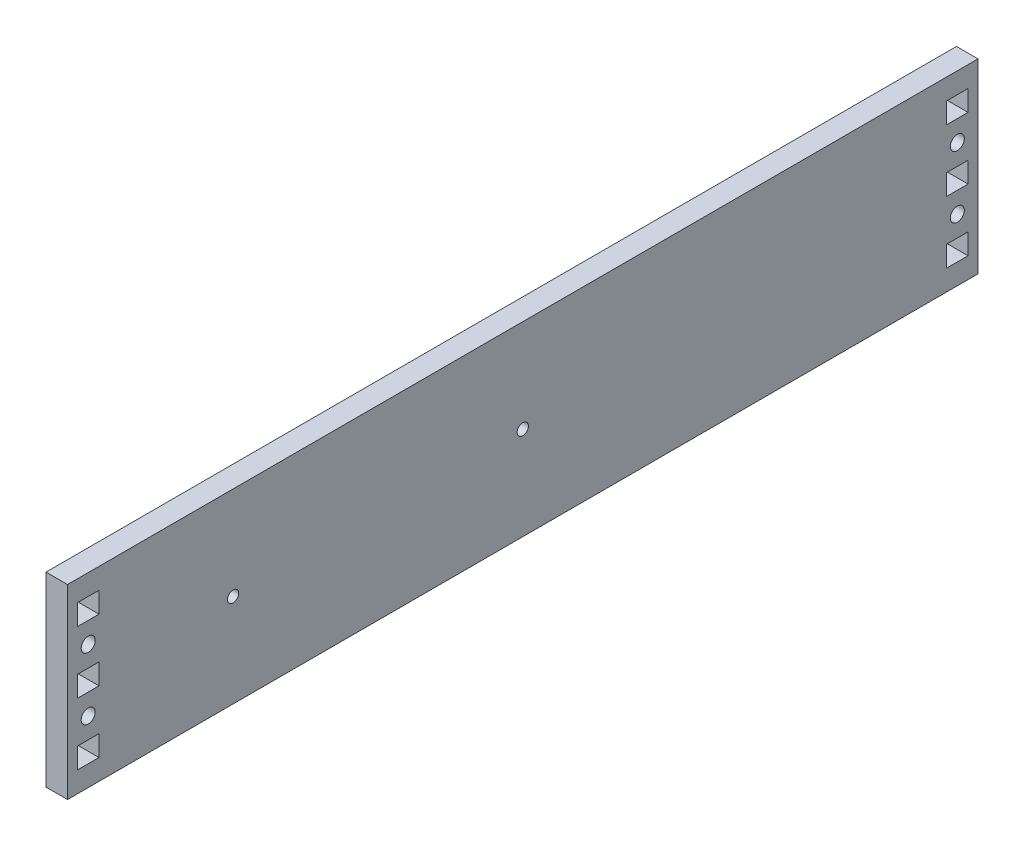
SolidWorks part; units mm, degrees
material "Acrylic (BLUE)"
ref_plane "Front Plane" through (0, 0, 0) normal (0, 0, 1) x (1, 0, 0)
ref_plane "Top Plane" through (0, 0, 0) normal (0, 1, 0) x (1, 0, 0)
ref_plane "Right Plane" through (0, 0, 0) normal (1, 0, 0) x (0, 0, -1)
sketch "Sketch1" plane through (0, 0, 0) normal (1, 0, 0) x (0, 0, -1)
  line L0 (0, 0) -> (0, 28.575) construction
  line L1 (-139.7, 28.575) -> (139.7, 28.575)
  line L2 (-139.7, 28.575) -> (-139.7, -28.575)
  line L3 (-139.7, -28.575) -> (139.7, -28.575)
  line L4 (139.7, 28.575) -> (139.7, -28.575)
  line L5 (-130.048, 0) -> (0, 0) construction
  line L6 (0, 0) -> (130.048, 0) construction
  line L7 (0, 0) -> (0, -28.575) construction
  line B0 (-130.048, 3.175) -> (-130.048, -3.175)
  line B1 (-130.048, -3.175) -> (-136.652, -3.175)
  line B2 (-136.652, -3.175) -> (-136.652, 3.175)
  line B3 (-136.652, 3.175) -> (-130.048, 3.175)
  line B4 (-130.048, 22.225) -> (-130.048, 15.875)
  line B5 (-130.048, 15.875) -> (-136.652, 15.875)
  line B6 (-136.652, 15.875) -> (-136.652, 22.225)
  line B7 (-136.652, 22.225) -> (-130.048, 22.225)
  circle B8 centre (-133.35, 9.525) radius 2.1526
  line B9 (-130.048, -15.875) -> (-130.048, -22.225)
  line B10 (-130.048, -22.225) -> (-136.652, -22.225)
  line B11 (-136.652, -15.875) -> (-136.652, -22.225)
  line B12 (-130.048, -15.875) -> (-136.652, -15.875)
  circle B13 centre (-133.35, -9.525) radius 2.1527
  line B14 (136.652, 3.175) -> (136.652, -3.175)
  line B15 (136.652, -3.175) -> (130.048, -3.175)
  line B16 (130.048, -3.175) -> (130.048, 3.175)
  line B17 (130.048, 3.175) -> (136.652, 3.175)
  line B18 (136.652, 22.225) -> (136.652, 15.875)
  line B19 (136.652, 15.875) -> (130.048, 15.875)
  line B20 (130.048, 15.875) -> (130.048, 22.225)
  line B21 (130.048, 22.225) -> (136.652, 22.225)
  circle B22 centre (133.35, 9.525) radius 2.1526
  line B23 (136.652, -15.875) -> (136.652, -22.225)
  line B24 (136.652, -22.225) -> (130.048, -22.225)
  line B25 (130.048, -15.875) -> (130.048, -22.225)
  line B26 (136.652, -15.875) -> (130.048, -15.875)
  circle B27 centre (133.35, -9.525) radius 2.1527
  dimension "D1" = 266.7
  dimension "D2" = 57.15
  dimension "D3" = 6.35
  dimension "D4" = 6.35
sketch_block_instance "BOLT_HOLE_2X-1"
sketch_block "BOLT_HOLE_2X" parameters "D1"=4.3053, "D2"=6.35, "D3"=6.35, "D4"=6.604
sketch_block_instance "BOLT_HOLE_2X-2"
extrude "Boss-Extrude1" add sketch "Sketch1" along normal blind 6.604
hole_wizard "CSK for #8 Flat Head Socket Cap Screw1" positions "Sketch3" profile "Sketch2" countersink size "#8" standard "ANSI Inch" end condition through all
sketch "Sketch3" plane through (0, 0, 0) normal (-1, 0, 0) x (0, 0, 1)
  point P0 (-133.35, 9.525)
  point P3 (-133.35, -9.525)
  point P6 (133.35, 9.525)
  point P9 (133.35, -9.525)
sketch "Sketch2" plane through (0, 9.525, -133.35) normal (0, 1, 0) x (0, 0, 1)
  line L0 (0, 0) -> (0, 6.604)
  line L1 (0, 6.604) -> (2.1526, 6.604)
  line L2 (2.1526, 6.604) -> (2.1526, 2.7685)
  line L3 (2.1526, 2.7685) -> (4.5593, 0)
  line L5 (4.5593, 0) -> (0, 0)
  line L6 (-2.1526, 2.7685) -> (-4.5593, 0) construction
  line L11 (0, -6.35) -> (0, 107.95) construction
  dimension "Thru Hole Dia." = 4.3053
  dimension "Thru Hole Depth" = 6.604
  dimension "Near C'Sink Dia." = 9.1186
  dimension "Near C'Sink Angle" = 82
hole_wizard "#8-32 Tapped Hole1" positions "Sketch7" profile "Sketch6" tap size "#8-32" standard "ANSI Inch"
sketch "Sketch7" plane through (0, 0, 0) normal (-1, 0, 0) x (0, 0, 1)
  line L0 (139.7, 0) -> (88.9, 0) construction
  line L1 (139.7, 28.575) -> (139.7, -28.575) construction
  line L2 (88.9, 0) -> (0, 0) construction
  point P0 (88.9, 0)
  point P2 (0, 0)
  dimension "D1" = 50.8
  dimension "D2" = 139.7
sketch "Sketch6" plane through (0, 0, 88.9) normal (0, 1, 0) x (0, 0, 1)
  line L0 (0, 0) -> (0, 11.7566)
  line L1 (0, 11.7566) -> (1.7272, 10.7188)
  line L2 (1.7272, 10.7188) -> (1.7272, 0)
  line L5 (1.7272, 0) -> (0, 0)
  line L10 (0, 11.7566) -> (-1.7272, 10.7188) construction
  line L11 (0, -6.35) -> (0, 107.95) construction
  dimension "Tap Drill Dia." = 3.4544
  dimension "Tap Drill Depth" = 10.7188
  dimension "Drill Angle" = 118
other "Move Face1" [suppressed] parameters "D1"=0.0508
